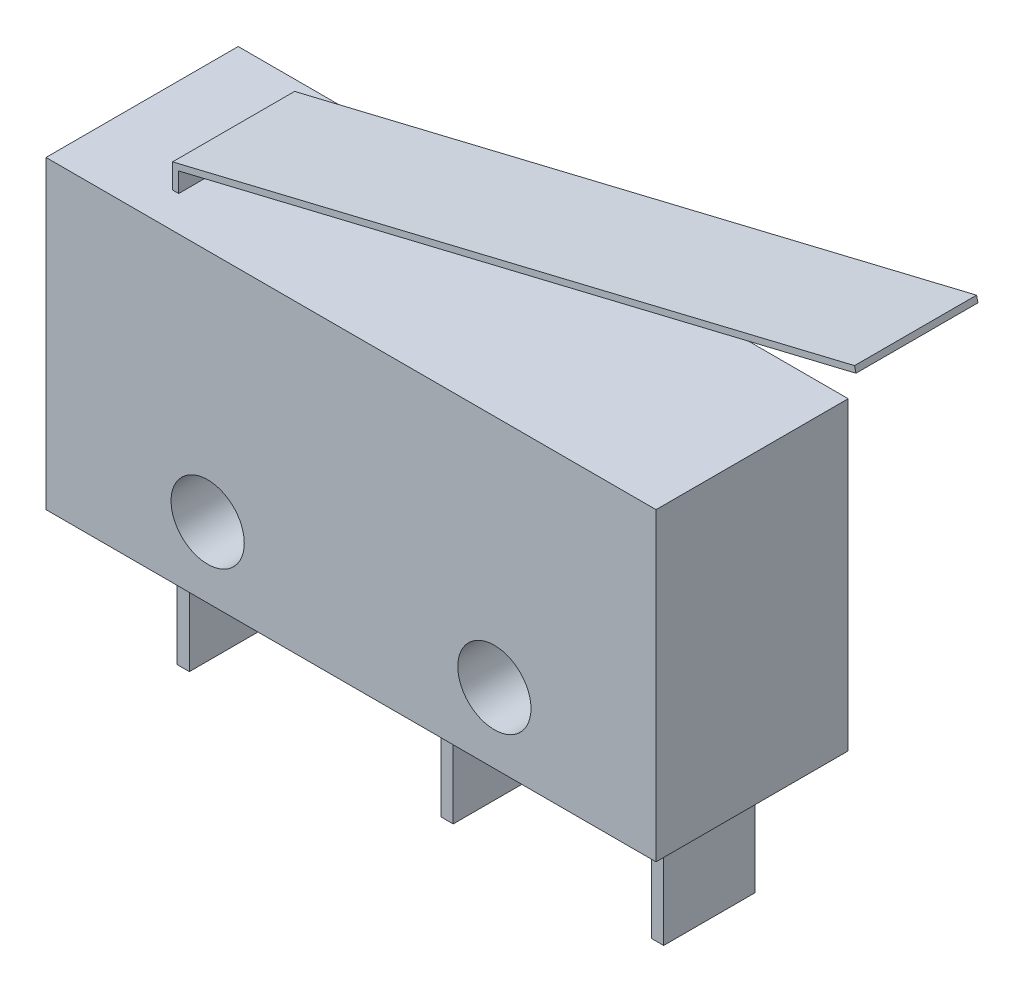
SolidWorks part; units mm, degrees
ref_plane "Plano frontal" through (0, 0, 0) normal (0, 0, 1) x (1, 0, 0)
ref_plane "Plano superior" through (0, 0, 0) normal (0, 1, 0) x (1, 0, 0)
ref_plane "Plano direito" through (0, 0, 0) normal (1, 0, 0) x (0, 0, -1)
sketch "Esboço1" plane through (0, 0, 0) normal (0, 0, 1) x (1, 0, 0)
  line L0 (1.7, -5) -> (8.2, -5)
  line L1 (-10, 5) -> (-7, 5)
  line L2 (-10, 5) -> (-10, -5)
  line L3 (-10, -5) -> (-7.35, -5)
  line L4 (10, 5) -> (10, -5)
  line L5 (-10, 5) -> (10, -5) construction
  line L6 (-10, -5) -> (10, 5) construction
  line L7 (-6.95, -5) -> (1.3, -5)
  line L8 (8.6, -5) -> (8.6, -8.9)
  line L9 (8.6, -8.9) -> (8.2, -8.9)
  line L10 (8.2, -5) -> (8.2, -8.9)
  line L11 (8.6, -5) -> (10, -5)
  line L12 (1.7, -5) -> (1.7, -8.9)
  line L13 (1.7, -8.9) -> (1.3, -8.9)
  line L14 (1.3, -5) -> (1.3, -8.9)
  line L15 (-6.8, 5.6425) -> (15.4054, 11)
  line L16 (-6.95, -5) -> (-6.95, -8.9)
  line L17 (-6.95, -8.9) -> (-7.35, -8.9)
  line L18 (-7.35, -5) -> (-7.35, -8.9)
  line L19 (15.4054, 11) -> (15.3584, 11.1944)
  line L20 (15.3584, 11.1944) -> (-7, 5.8)
  line L21 (-7, 5.8) -> (-7, 5)
  line L22 (-6.8, 5.6425) -> (-6.8, 5)
  line L23 (-6.8, 5) -> (10, 5)
  line L24 (-7, 5) -> (-6.8, 5) construction
  line L25 (0, 0) -> (0, -3.6561) construction
  circle A0 centre (-4.7, -2.7) radius 1.2
  circle A1 centre (4.7, -2.7) radius 1.2
  point P0 (0, 0)
  dimension "D13" = 2.4
  dimension "D14" = 7
  dimension "D15" = 6.5
  dimension "D1" = 20
  dimension "D2" = 10
  dimension "D3" = 1.4
  dimension "D4" = 6.5
  dimension "D5" = 8.25
  dimension "D6" = 0.4
  dimension "D7" = 3.9
  dimension "D8" = 3
  dimension "D9" = 0.2
  dimension "D10" = 0.8
  dimension "D11" = 23
  dimension "D12" = 6
extrude "Ressalto-extrusão1" add sketch "Esboço1" along normal blind 6.3
sketch "Esboço2" plane through (10, 0, 0) normal (1, 0, 0) x (0, 0, -1)
  line L0 (-3.15, -8.9) -> (-3.15, -5) construction
  line L1 (-6.3, -8.9) -> (0, -8.9) construction
  line L2 (0, -8.9) -> (-1.65, -8.9)
  line L3 (-6.3, -5) -> (0, -5) construction
  line L4 (0, -5) -> (0, -8.9)
  line L5 (-1.65, -5) -> (0, -5)
  line L6 (-1.65, -8.9) -> (-1.65, -5)
  line L7 (-4.65, -8.9) -> (-4.65, -5)
  line L8 (-4.65, -5) -> (-6.3, -5)
  line L9 (-6.3, -5) -> (-6.3, -8.9)
  line L10 (-6.3, -8.9) -> (-4.65, -8.9)
  point P5 (-3.15, -8.9)
  dimension "D1" = 3
extrude "Corte-extrusão1" cut sketch "Esboço2" against normal through all
sketch "Esboço3" plane through (-7, 0, 0) normal (-1, 0, 0) x (0, 0, 1)
  line L0 (1.15, 5) -> (1.15, 11.1944)
  line L1 (6.3, 5) -> (0, 5) construction
  line L2 (6.3, 11.1944) -> (0, 11.1944) construction
  line L3 (1.15, 11.1944) -> (0, 11.1944)
  line L4 (0, 11.1944) -> (0, 5)
  line L5 (0, 5) -> (1.15, 5)
  line L6 (3.15, 5) -> (3.15, 11.706) construction
  line L7 (6.3, 5) -> (5.15, 5)
  line L8 (6.3, 11.1944) -> (6.3, 5)
  line L9 (5.15, 11.1944) -> (6.3, 11.1944)
  line L10 (5.15, 5) -> (5.15, 11.1944)
  dimension "D1" = 4
extrude "Corte-extrusão2" cut sketch "Esboço3" against normal through all
